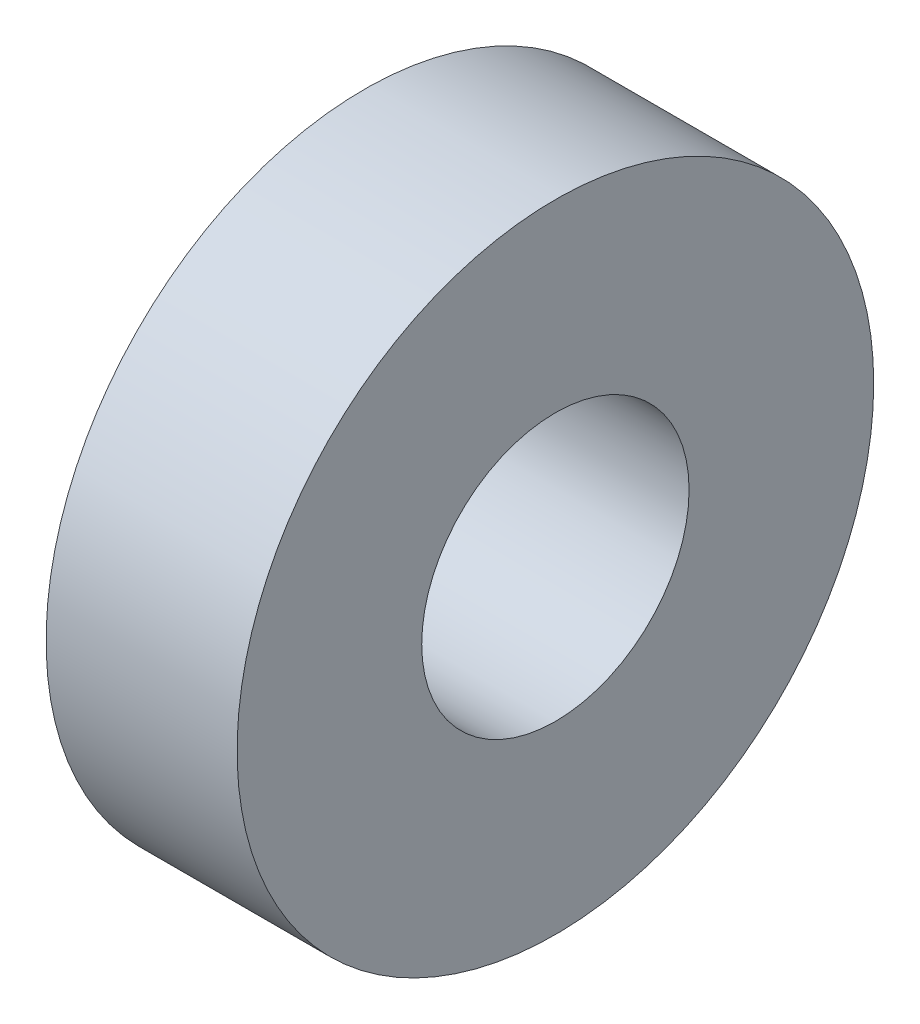
SolidWorks part; units mm, degrees
ref_plane "Plan de face" through (0, 0, 0) normal (0, 0, 1) x (1, 0, 0)
ref_plane "Plan de dessus" through (0, 0, 0) normal (0, 1, 0) x (1, 0, 0)
ref_plane "Plan de droite" through (0, 0, 0) normal (1, 0, 0) x (0, 0, -1)
sketch "Esquisse1" plane through (0, 0, 0) normal (1, 0, 0) x (0, 0, -1)
  circle A0 centre (0, 0) radius 5
  circle A1 centre (0, 0) radius 2.1
  dimension "D1" = 10
  dimension "D2" = 4.2
extrude "Extrusion1" add sketch "Esquisse1" along normal blind 3
